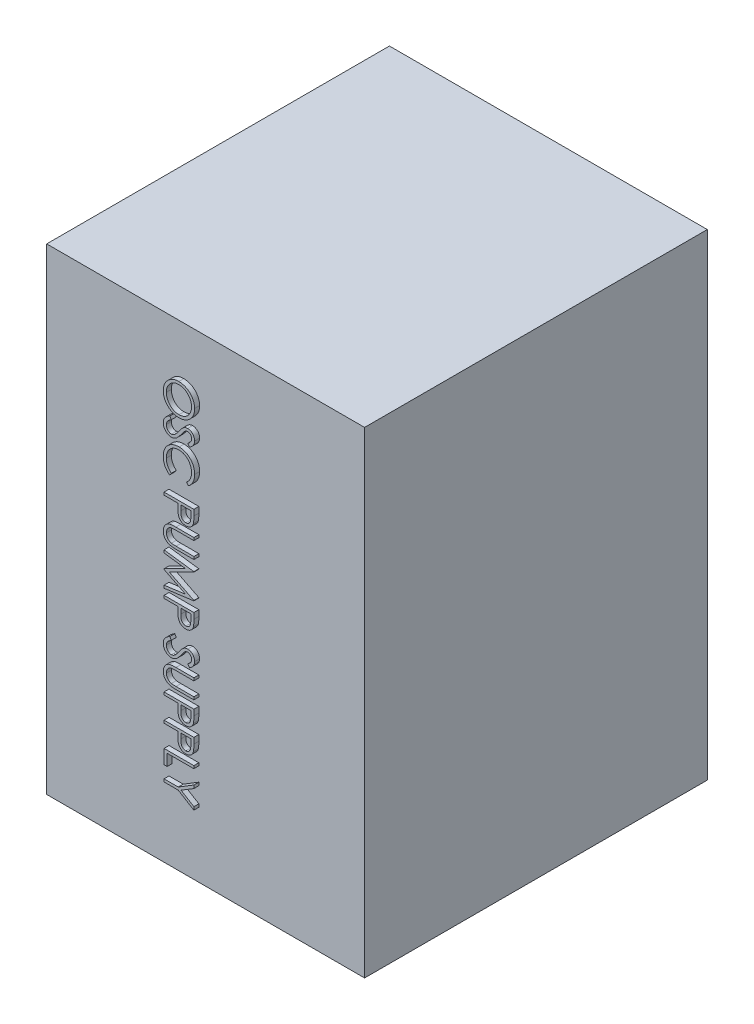
SolidWorks part; units mm, degrees
ref_plane "Front Plane" through (0, 0, 0) normal (0, 0, 1) x (1, 0, 0)
ref_plane "Top Plane" through (0, 0, 0) normal (0, 1, 0) x (1, 0, 0)
ref_plane "Right Plane" through (0, 0, 0) normal (1, 0, 0) x (0, 0, -1)
sketch "Sketch1" plane through (0, 0, 0) normal (0, 0, 1) x (1, 0, 0)
  line L1 (0, 0) -> (-320, 0)
  line L2 (0, 0) -> (0, 480)
  line L3 (0, 480) -> (-320, 480)
  line L4 (-320, 0) -> (-320, 480)
  dimension "D1" = 320
  dimension "D2" = 480
extrude "Boss-Extrude1" add sketch "Sketch1" along normal blind 345
sketch "Sketch2" plane through (0, 0, 345) normal (0, 0, 1) x (1, 0, 0)
  line L0 (-196.8577, 480) -> (-196.8577, 0) construction
  line L2 (0, 480) -> (-320, 480) construction
  text T0 "    OSC PUMP SUPPLY" font "Century Gothic" height 30
extrude "Boss-Extrude3" add sketch "Sketch2" along normal blind 5
